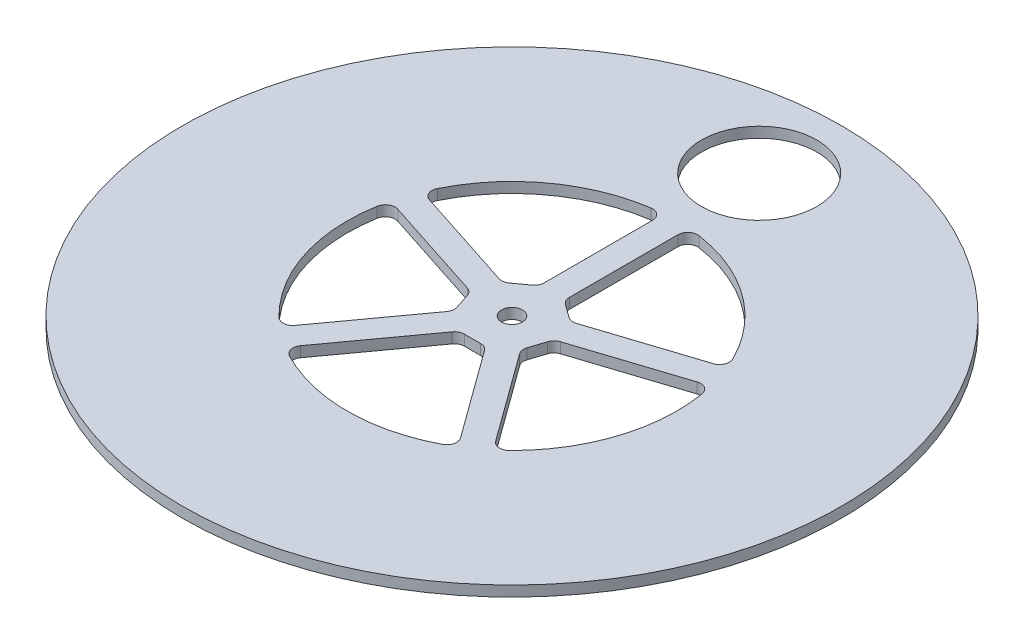
SolidWorks part; units mm, degrees
material "Acrylic (Medium-high impact)"
ref_plane "Front Plane" through (0, 0, 0) normal (0, 0, 1) x (1, 0, 0)
ref_plane "Top Plane" through (0, 0, 0) normal (0, 1, 0) x (1, 0, 0)
ref_plane "Right Plane" through (0, 0, 0) normal (1, 0, 0) x (0, 0, -1)
sketch "Sketch1" plane through (0, 0, 0) normal (0, 1, 0) x (1, 0, 0)
  circle A1 centre (0, 0) radius 100
  dimension "D1" = 200
extrude "Boss-Extrude1" add sketch "Sketch1" along normal blind 3.175
sketch "Sketch2" plane through (0, 3.175, 0) normal (0, 1, 0) x (1, 0, 0)
  circle A0 centre (0, 75) radius 17.5
  dimension "D1" = 35
  dimension "D2" = 75
extrude "Cut-Extrude1" cut sketch "Sketch2" against normal through all
sketch "Sketch3" plane through (0, 3.175, 0) normal (0, 1, 0) x (1, 0, 0)
  circle A0 centre (0, 0) radius 3.175
  dimension "D1" = 6.35
extrude "Cut-Extrude2" cut sketch "Sketch3" against normal blind 10
sketch "Sketch4" plane through (0, 3.175, 0) normal (0, 1, 0) x (1, 0, 0)
  line L0 (3.8174, 49.8541) -> (3.8174, 12.0593)
  line L1 (3.8174, 12.0593) -> (10.2895, 7.3571)
  line L2 (10.2895, 7.3571) -> (46.2344, 19.0363)
  line L3 (0, 0) -> (29.3893, 40.4508) construction
  line L4 (0, 0) -> (0, 30.5831) construction
  arc A0 (3.8174, 49.8541) -> (46.2344, 19.0363) centre (0, 0) cw
  circle A1 centre (0, 0) radius 100 construction
  point P7 (7.0534, 9.7082)
  point P9 (29.3893, 40.4508)
  dimension "D2" = 50
  dimension "D1" = 72
  dimension "D3" = 36
  dimension "D4" = 8
  dimension "D5" = 12
extrude "Cut-Extrude3" cut sketch "Sketch4" against normal up to next (3.175 mm away)
fillet "Fillet1" radius 3 4 edges at (3.8174, 1.5875, -12.0593) (10.2895, 1.5875, -7.3571) (46.2344, 1.5875, -19.0363) (3.8174, 1.5875, -49.8541)
pattern_circular "CirPattern1" count 5 over 360 about axis through (0, 0, 0) along (0, 1, 0) of "Cut-Extrude3", "Fillet1"
